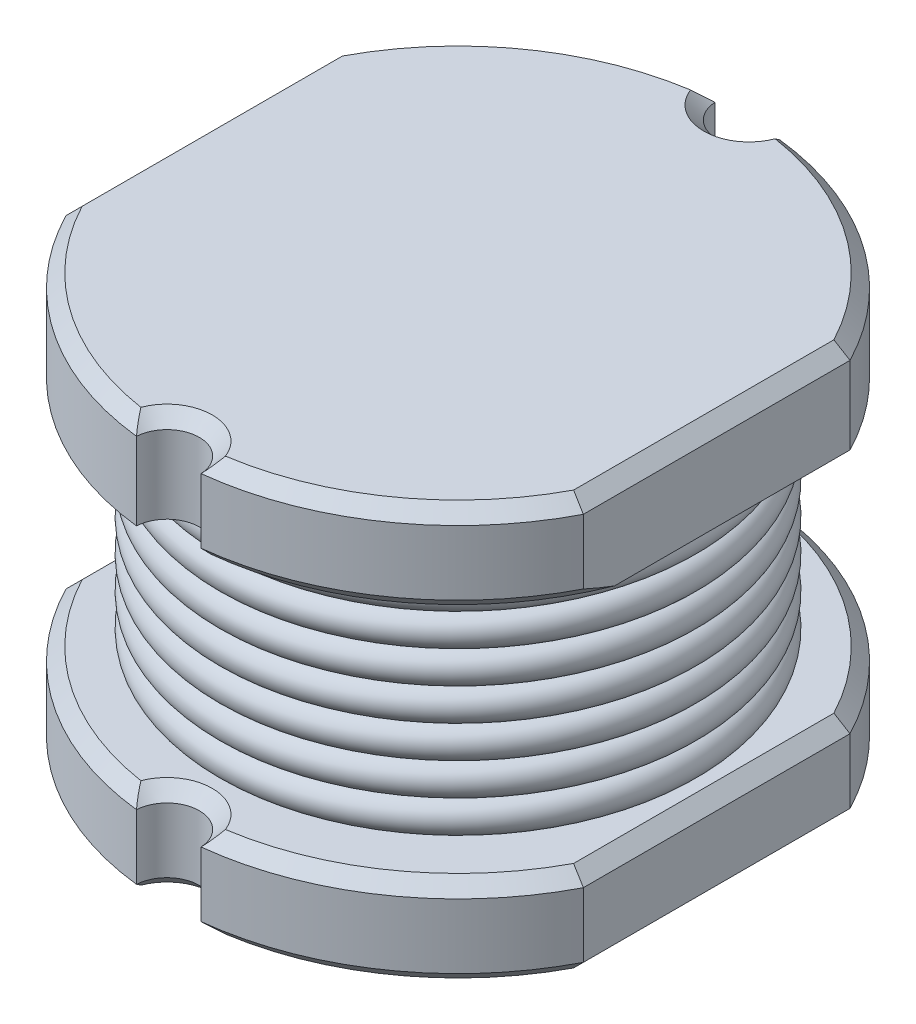
SolidWorks part; units mm, degrees
ref_plane "Front Plane" through (0, 0, 0) normal (0, 0, 1) x (1, 0, 0)
ref_plane "Top Plane" through (0, 0, 0) normal (0, 1, 0) x (1, 0, 0)
ref_plane "Right Plane" through (0, 0, 0) normal (1, 0, 0) x (0, 0, -1)
sketch "Sketch1" plane through (0, 0, 0) normal (0, 1, 0) x (1, 0, 0)
  circle A0 centre (0, 0) radius 2.25
  dimension "D1" = 4.5
extrude "BASE" add sketch "Sketch1" along normal blind 0.7
sketch "Sketch2" plane through (0, 0.7, 0) normal (0, 1, 0) x (1, 0, 0)
  circle A0 centre (0, 0) radius 1.5
  dimension "D1" = 3
extrude "COIL ENCOMPASSMENT" add sketch "Sketch2" along normal blind 1.8
sketch "Sketch3" plane through (0, 2.5, 0) normal (0, 1, 0) x (1, 0, 0)
  circle A0 centre (0, 0) radius 2.25
  dimension "D1" = 4.5
extrude "TOP BASE" add sketch "Sketch3" along normal blind 0.7
sketch "Sketch5" plane through (0, 3.2, 0) normal (0, 1, 0) x (1, 0, 0)
  line L0 (0, -2.25) -> (0, 2.25) construction
  circle A0 centre (0, -2.25) radius 0.25
  circle A1 centre (0, 0) radius 2.25 construction
  circle A2 centre (0, 2.25) radius 0.25
  dimension "D1" = 0.5
extrude "SIDE CUTS FOR BASES" cut sketch "Sketch5" against normal up to surface (3.2 mm away) up to face at (0, 0, 2.25)
sketch "Sketch98" plane through (0, 3.2, 0) normal (0, 1, 0) x (1, 0, 0)
  line L1 (-2, -1.0308) -> (-2.25, -1.0308)
  line L2 (-2, -1.0308) -> (-2, 1.0308)
  line L3 (-2, 1.0308) -> (-2.25, 1.0308)
  line L4 (-2.25, -1.0308) -> (-2.25, 1.0308)
  line L5 (-2, -1.0308) -> (-2.25, 1.0308) construction
  line L6 (-2, 1.0308) -> (-2.25, -1.0308) construction
  arc A0 (-0.2496, 2.2361) -> (-0.2496, -2.2361) centre (0, 0) ccw construction
  point P0 (-2, -1.0308)
  dimension "D1" = 2
extrude "BASE SIDES" cut sketch "Sketch98" against normal through all
mirror "BS M" about plane through (0, 0, 0) normal (1, 0, 0) of "BASE SIDES"
ref_plane "COIL START" through (0, 0.825, 0) normal (0, 1, 0) x (1, 0, 0)
sketch "Sketch6" plane through (0, 0.825, 0) normal (0, 1, 0) x (1, 0, 0)
  circle A0 centre (0, 0) radius 1.75
  dimension "D1" = 3.5
sweep "COIL" add path "Sketch6" circular profile diameter 0.25 parameters "D3"=0.25
pattern_linear "COIL P" count 7 spacing 0.25 along (0, 1, 0) of "COIL"
chamfer "BASES C" distance 0.1 angle 45 27 edges at (0, 0.7, 1.5) (1.2761, 0.7, 1.8531) (1.2761, 0.7, -1.8531) (-1.2761, 0.7, -1.8531) (-1.2761, 0.7, 1.8531) (0, 0.7, 2) (0, 0.7, -2) (1.2761, 2.5, 1.8531) (-1.2761, 2.5, -1.8531) (0, 0, 2) (1.2761, 0, 1.8531) (-1.2761, 0, 1.8531) (0, 0, -2) (-1.2761, 0, -1.8531) (1.2761, 0, -1.8531) (1.2761, 3.2, 1.8531) (1.2761, 3.2, -1.8531) (-1.2761, 3.2, -1.8531) (-1.2761, 3.2, 1.8531) (0, 3.2, 2) (0, 3.2, -2) (-2, 3.2, 0) (2, 3.2, 0) (-2, 0, 0) (2, 0, 0) (-2, 0.7, 0) (2, 0.7, 0)
